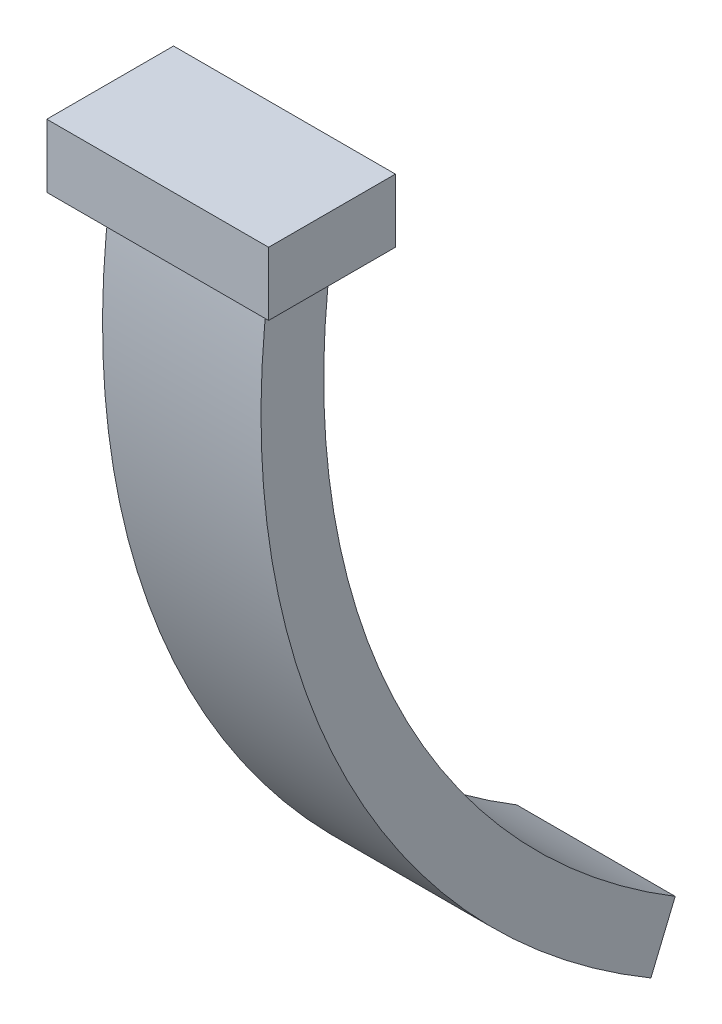
SolidWorks part; units mm, degrees
ref_plane "Ön Düzlem" through (0, 0, 0) normal (0, 0, 1) x (1, 0, 0)
ref_plane "Üst Düzlem" through (0, 0, 0) normal (0, 1, 0) x (1, 0, 0)
ref_plane "Sağ Düzlem" through (0, 0, 0) normal (1, 0, 0) x (0, 0, -1)
sketch "Çizim1" plane through (0, 0, 0) normal (0, 1, 0) x (1, 0, 0)
  line L1 (0, 0) -> (5, 0)
  line L2 (0, 0) -> (0, 2)
  line L3 (0, 2) -> (5, 2)
  line L4 (5, 0) -> (5, 2)
  dimension "D1" = 5
  dimension "D2" = 2
sketch "Çizim2" plane through (0, 0, 0) normal (1, 0, 0) x (0, 0, -1)
  line L0 (0, 0) -> (2, 0) construction
  arc A0 (0, 0) -> (12.0628, -25) centre (24.7589, -3.4638) ccw
  dimension "D1" = 25
  dimension "D2" = 25
sweep "Süpür1" add profiles "Çizim1" path "Çizim2"
sketch "Çizim3" plane through (0, 0, 0) normal (0, 1, 0) x (1, 0, 0)
  line L0 (-1, 3) -> (-1, -1)
  line L5 (-1, -1) -> (6, -1)
  line L6 (6, -1) -> (6, 3)
  line L7 (6, 3) -> (-1, 3)
  line L8 (0, 2) -> (0, 0)
  line L9 (0, 0) -> (5, 0)
  line L10 (5, 0) -> (5, 2)
  line L11 (5, 2) -> (0, 2)
  line L12 (0, 2) -> (0, 0)
  line L13 (0, 0) -> (5, 0)
  line L14 (5, 0) -> (5, 2)
  line L15 (5, 2) -> (0, 2)
  line M13 (0, 2) -> (0, 0)
  line M14 (0, 0) -> (5, 0)
  line M15 (5, 0) -> (5, 2)
  line M16 (5, 2) -> (0, 2)
  dimension "D1" = 0
  dimension "D2" = 1
extrude "Yükseklik-Ekstrüzyon1" add sketch "Çizim3" along normal blind 2 contours M16 M13 M14 M15 | L6 L7 L0 L5 M13 M16 M15 M14 | L12 L13 L14 L15
